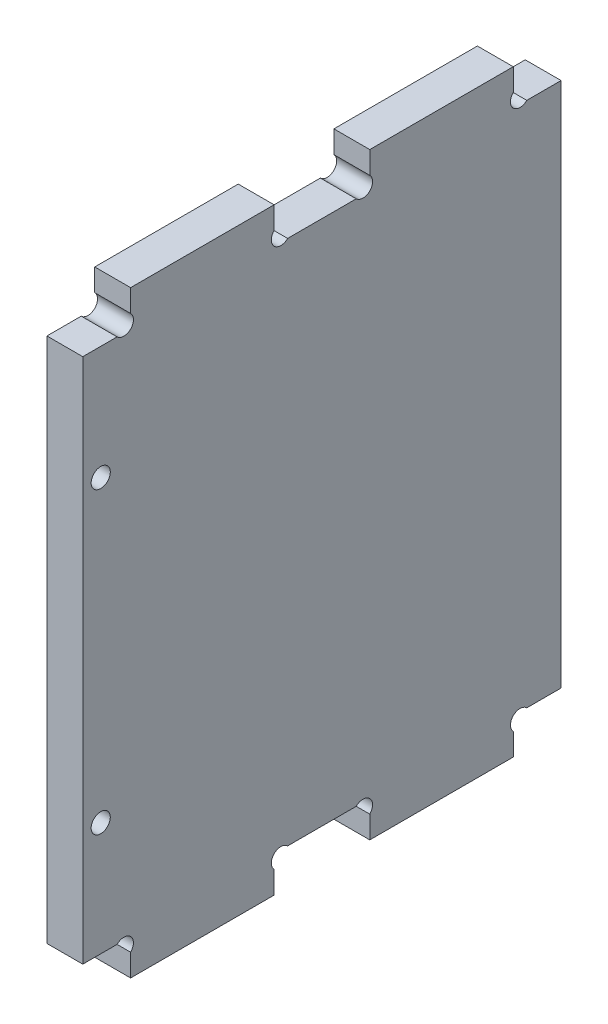
SolidWorks part; units mm, degrees
ref_plane "Plan de face" through (0, 0, 0) normal (0, 0, 1) x (1, 0, 0)
ref_plane "Plan de dessus" through (0, 0, 0) normal (0, 1, 0) x (1, 0, 0)
ref_plane "Plan de droite" through (0, 0, 0) normal (1, 0, 0) x (0, 0, -1)
sketch "Esquisse1" plane through (0, 0, 0) normal (1, 0, 0) x (0, 0, -1)
  line L0 (40, 114.5511) -> (40, -14.9803) construction
  line L1 (0, 0) -> (80, 0) construction
  line L2 (0, 0) -> (0, 100) construction
  line L3 (0, 100) -> (80, 100) construction
  line L4 (80, 0) -> (80, 100) construction
  line L5 (-10.7408, 94) -> (90.0863, 94) construction
  line L6 (-25.6937, 50) -> (88.3435, 50) construction
  line L7 (8, 104.227) -> (8, 91.468) construction
  line L8 (32, 104.227) -> (32, 91.468) construction
  line L9 (20, 96.861) -> (20, 92.3626) construction
  line L10 (8, 94) -> (-4.2853, 106.2853) construction
  line L11 (0, 94) -> (5.7373, 94)
  line L12 (8, 96.2627) -> (8, 100)
  line L13 (8, 100) -> (32, 100)
  line L14 (32, 100) -> (32, 96.2627)
  line L15 (48, 100) -> (48, 96.2627)
  line L16 (72, 100) -> (48, 100)
  line L17 (72, 96.2627) -> (72, 100)
  line L18 (80, 94) -> (74.2627, 94)
  line L19 (34.2627, 94) -> (45.7373, 94)
  line L20 (34.2627, 6) -> (45.7373, 6)
  line L21 (80, 6) -> (74.2627, 6)
  line L22 (72, 3.7373) -> (72, 0)
  line L23 (72, 0) -> (48, 0)
  line L24 (48, 0) -> (48, 3.7373)
  line L25 (32, 0) -> (32, 3.7373)
  line L26 (8, 0) -> (32, 0)
  line L27 (8, 3.7373) -> (8, 0)
  line L28 (0, 6) -> (5.7373, 6)
  line L29 (80, 94) -> (80, 6)
  line L30 (0, 6) -> (0, 94)
  line L31 (3, -3.2382) -> (3, 37.3765) construction
  line L32 (-12.9652, 25) -> (16.6332, 25) construction
  arc A0 (5.7373, 94) -> (8, 96.2627) centre (6.8686, 95.1314) ccw
  arc A1 (34.2627, 94) -> (32, 96.2627) centre (33.1314, 95.1314) cw
  arc A2 (45.7373, 94) -> (48, 96.2627) centre (46.8686, 95.1314) ccw
  arc A3 (74.2627, 94) -> (72, 96.2627) centre (73.1314, 95.1314) cw
  arc A4 (74.2627, 6) -> (72, 3.7373) centre (73.1314, 4.8686) ccw
  arc A5 (45.7373, 6) -> (48, 3.7373) centre (46.8686, 4.8686) cw
  arc A6 (34.2627, 6) -> (32, 3.7373) centre (33.1314, 4.8686) ccw
  arc A7 (5.7373, 6) -> (8, 3.7373) centre (6.8686, 4.8686) cw
  circle A8 centre (3, 25) radius 1.6
  circle A9 centre (3, 75) radius 1.6
  dimension "D5" = 6
  dimension "D1" = 8
  dimension "D2" = 24
  dimension "D3" = 12
  dimension "D4" = 45
extrude "Extrusion1" add sketch "Esquisse1" along normal blind 6
